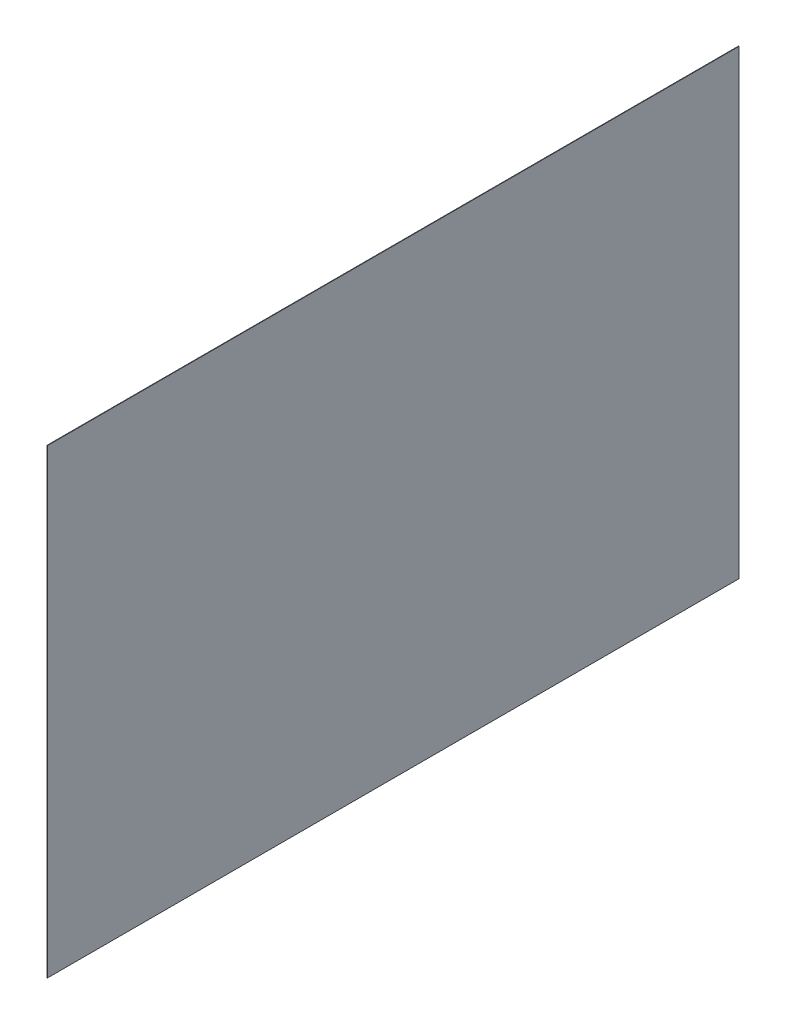
SolidWorks part; units mm, degrees
material "Teak"
ref_plane "Front Plane" through (0, 0, 0) normal (0, 0, 1) x (1, 0, 0)
ref_plane "Top Plane" through (0, 0, 0) normal (0, 1, 0) x (1, 0, 0)
ref_plane "Right Plane" through (0, 0, 0) normal (1, 0, 0) x (0, 0, -1)
sketch "Sketch1" plane through (0, 0, 0) normal (1, 0, 0) x (0, 0, -1)
  line L1 (-1828.8, -1219.2) -> (1828.8, -1219.2)
  line L2 (-1828.8, -1219.2) -> (-1828.8, 1219.2)
  line L3 (-1828.8, 1219.2) -> (1828.8, 1219.2)
  line L4 (1828.8, -1219.2) -> (1828.8, 1219.2)
  line L5 (-1828.8, -1219.2) -> (1828.8, 1219.2) construction
  line L6 (-1828.8, 1219.2) -> (1828.8, -1219.2) construction
  point P0 (0, 0)
  dimension "D1" = 3657.6
  dimension "D2" = 2438.4
extrude "Boss-Extrude1" add sketch "Sketch1" along normal blind 2.54
equation "\"D1@Sketch1\"=8ft+1ft+3ft"
equation "\"D2@Sketch1\"=6ft+2ft"
